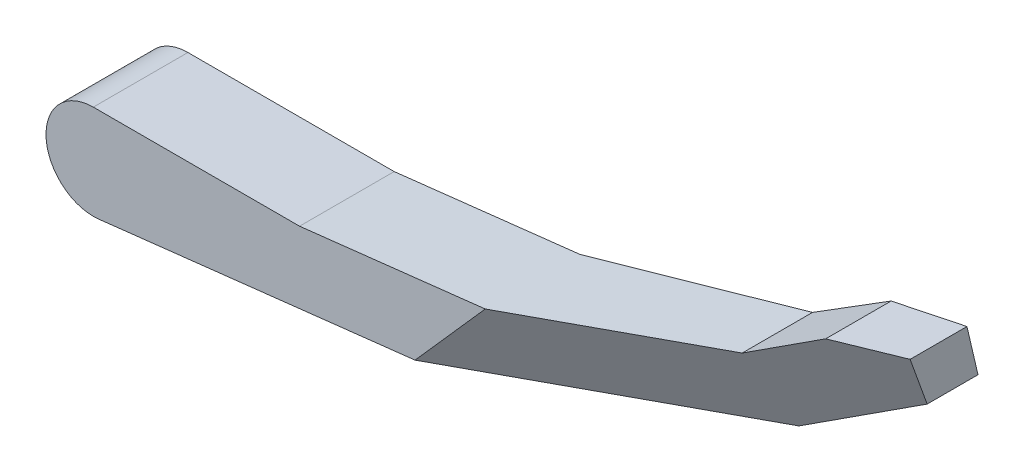
SolidWorks part; units mm, degrees
ref_plane "前视基准面" through (0, 0, 0) normal (0, 0, 1) x (1, 0, 0)
ref_plane "上视基准面" through (0, 0, 0) normal (0, 1, 0) x (1, 0, 0)
ref_plane "右视基准面" through (0, 0, 0) normal (1, 0, 0) x (0, 0, -1)
sketch "草图2" plane through (0, 0, 0) normal (0, 0, 1) x (1, 0, 0)
  line L0 (0.4528, -3.9743) -> (50.959, 1.7802)
  line L1 (50.959, 1.7802) -> (60, 7)
  line L2 (60, 7) -> (60, 11)
  line L3 (60, 11) -> (54.9282, 11)
  line L4 (54.9282, 11) -> (49.0398, 7.6003)
  line L5 (49.0398, 7.6003) -> (17.4402, 4)
  line L6 (17.4402, 4) -> (0, 4)
  arc A0 (0.4528, -3.9743) -> (0, 4) centre (0, 0) cw
  point P4 (32.2316, -0.9941)
  point P11 (45.1667, -1.564)
  dimension "D1" = 4
  dimension "D2" = 11
  dimension "D3" = 4
  dimension "D4" = 60
  dimension "D5" = 30
  dimension "D6" = 6.5
  dimension "D7" = 6
  dimension "D8" = 6
extrude "凸台-拉伸1" add sketch "草图2" against normal blind 8 from offset 3 offset against normal yes
sketch "草图3" plane through (0, 0, -11) normal (0, 0, -1) x (-1, 0, 0)
  line L0 (-33.1427, 5.7891) -> (-27.2011, -0.9267)
  line L7 (0, 4) -> (-17.4402, 4)
  line L8 (-17.4402, 4) -> (-49.0398, 7.6003)
  line L9 (-49.0398, 7.6003) -> (-54.9282, 11)
  line L10 (-54.9282, 11) -> (-60, 11)
  line L11 (-60, 11) -> (-60, 7)
  line L12 (-60, 7) -> (-50.959, 1.7802)
  line L13 (-50.959, 1.7802) -> (-0.4528, -3.9743)
  line L14 (0, 4) -> (-17.4402, 4)
  line L15 (-17.4402, 4) -> (-49.0398, 7.6003)
  line L16 (-49.0398, 7.6003) -> (-54.9282, 11)
  line L17 (-54.9282, 11) -> (-60, 11)
  line L18 (-60, 11) -> (-60, 7)
  line L19 (-60, 7) -> (-50.959, 1.7802)
  line L20 (-50.959, 1.7802) -> (-0.4528, -3.9743)
  arc A1 (-0.4528, -3.9743) -> (0, 4) centre (0, 0) ccw
  arc A2 (-0.4528, -3.9743) -> (0, 4) centre (0, 0) ccw
  line M3 (-17.4402, 4) -> (-49.0398, 7.6003)
  line M4 (-49.0398, 7.6003) -> (-54.9282, 11)
  line M5 (-54.9282, 11) -> (-60, 11)
  line M6 (-60, 11) -> (-60, 7)
  line M7 (-60, 7) -> (-50.959, 1.7802)
  line M8 (-50.959, 1.7802) -> (-0.4528, -3.9743)
  dimension "D2" = 42
  dimension "D3" = 16
  dimension "D1" = 0
extrude "凸台-拉伸2" add sketch "草图3" along normal blind 8 contours L0 M3 M4 M5 M6 M7 M8
sketch "草图4" plane through (0.4528, -3.9743, 0) normal (0.1132, -0.9936, 0) x (0.9936, 0.1132, 0)
  line L0 (26.9213, -11) -> (26.9213, -19)
  line L1 (26.9213, -19) -> (60.8595, -19)
  line L2 (60.8595, -19) -> (26.9213, -11)
  line L3 (26.9213, -3) -> (60.8595, -15.3525)
  line L4 (0, -3) -> (50.8329, -3) construction
  line L5 (60.8595, -19) -> (60.8595, -3) construction
  line L6 (60.8595, -15.3525) -> (60.8595, -3)
  line L7 (60.8595, -3) -> (26.9213, -3)
  dimension "D1" = 20
  dimension "D2" = 8
extrude "切除-拉伸1" cut sketch "草图4" along direction (-0.6626, -0.749, 0) on the side against the normal through all
